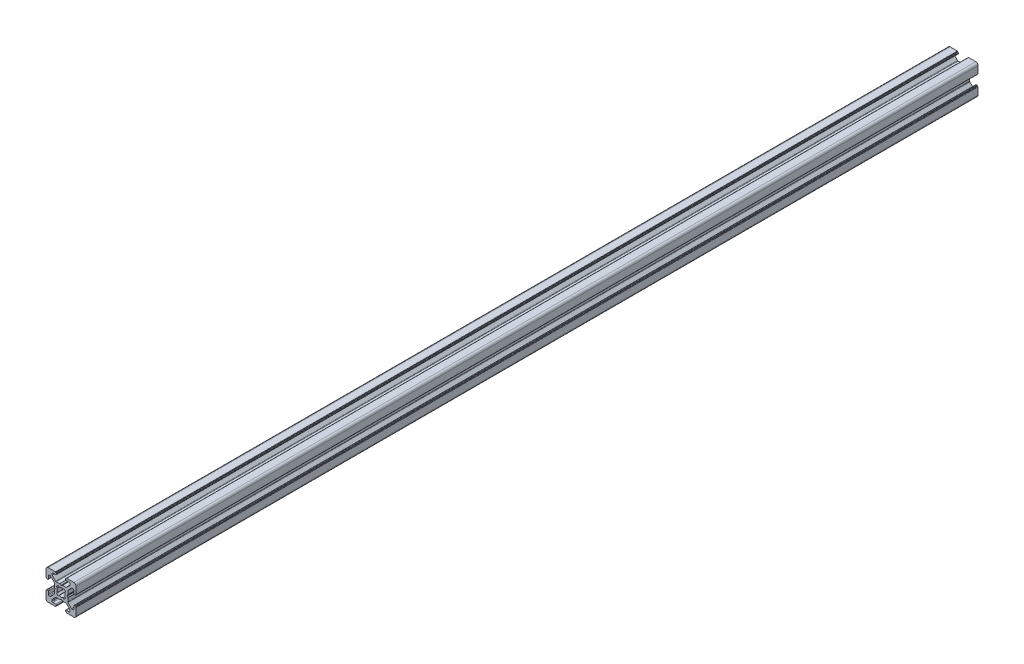
SolidWorks part; units mm, degrees
ref_plane "Front Plane" through (0, 0, 0) normal (0, 0, 1) x (1, 0, 0)
ref_plane "Top Plane" through (0, 0, 0) normal (0, 1, 0) x (1, 0, 0)
ref_plane "Right Plane" through (0, 0, 0) normal (1, 0, 0) x (0, 0, -1)
sketch "Sketch1" plane through (0, 0, 0) normal (0, 0, 1) x (1, 0, 0)
  line L0 (0, 13.3675) -> (0, -10.9159) construction
  line L1 (-12.9725, 0) -> (15.1887, 0) construction
  line L2 (-3.5, 8.5) -> (-5.5, 8.5)
  line L3 (-3.55, 9.7) -> (-3.55, 9.8)
  line L4 (-6, 7.2678) -> (-6, 8)
  line L5 (-7.2678, 6) -> (-8, 6)
  line L6 (-3.75, 10) -> (-8.5, 10)
  line L7 (-9.7, 3.55) -> (-9.8, 3.55)
  line L8 (-9.5, 3.2) -> (-9.5, 3.35)
  line L9 (-9, 3) -> (-9.3, 3)
  line L10 (-4.4732, 0.8536) -> (-4.0381, 0.1)
  line L11 (-4.5, 3.2322) -> (-4.5, 0.9536)
  line L12 (-8.5, 3.5) -> (-8.5, 5.5)
  line L13 (-10, 3.75) -> (-10, 8.5)
  line L14 (-3.5858, 4.6464) -> (-5.8536, 6.9142)
  line L15 (-4.6464, 3.5858) -> (-6.9142, 5.8536)
  line L16 (-3.2, 9.5) -> (-3.35, 9.5)
  line L17 (-3, 9) -> (-3, 9.3)
  line L18 (-0.8536, 4.4732) -> (-0.1, 4.0381)
  line L19 (-3.2322, 4.5) -> (-0.9536, 4.5)
  line L20 (-1.2582, 2.4453) -> (-1.9139, 2.9896)
  line L21 (-2.4453, 1.2582) -> (-2.9922, 1.9099)
  line L22 (3.5, -8.5) -> (5.5, -8.5)
  line L23 (3.55, -9.7) -> (3.55, -9.8)
  line L24 (6, -7.2678) -> (6, -8)
  line L25 (7.2678, -6) -> (8, -6)
  line L26 (3.75, -10) -> (8.5, -10)
  line L27 (9.7, -3.55) -> (9.8, -3.55)
  line L28 (9.5, -3.2) -> (9.5, -3.35)
  line L29 (9, -3) -> (9.3, -3)
  line L30 (4.4732, -0.8536) -> (4.0381, -0.1)
  line L31 (4.5, -3.2322) -> (4.5, -0.9536)
  line L32 (8.5, -3.5) -> (8.5, -5.5)
  line L33 (10, -3.75) -> (10, -8.5)
  line L34 (3.5858, -4.6464) -> (5.8536, -6.9142)
  line L35 (4.6464, -3.5858) -> (6.9142, -5.8536)
  line L36 (3.2, -9.5) -> (3.35, -9.5)
  line L37 (3, -9) -> (3, -9.3)
  line L38 (0.8536, -4.4732) -> (0.1, -4.0381)
  line L39 (3.2322, -4.5) -> (0.9536, -4.5)
  line L40 (1.2582, -2.4453) -> (1.9139, -2.9896)
  line L41 (2.4453, -1.2582) -> (2.9922, -1.9099)
  line L42 (-2.4453, -1.2582) -> (-2.9922, -1.9099)
  line L43 (-1.2582, -2.4453) -> (-1.9139, -2.9896)
  line L44 (-3.2322, -4.5) -> (-0.9536, -4.5)
  line L45 (-0.8536, -4.4732) -> (-0.1, -4.0381)
  line L46 (-3, -9) -> (-3, -9.3)
  line L47 (-3.2, -9.5) -> (-3.35, -9.5)
  line L48 (-4.6464, -3.5858) -> (-6.9142, -5.8536)
  line L49 (-3.5858, -4.6464) -> (-5.8536, -6.9142)
  line L50 (-10, -3.75) -> (-10, -8.5)
  line L51 (-8.5, -3.5) -> (-8.5, -5.5)
  line L52 (-4.5, -3.2322) -> (-4.5, -0.9536)
  line L53 (-4.4732, -0.8536) -> (-4.0381, -0.1)
  line L54 (-9, -3) -> (-9.3, -3)
  line L55 (-9.5, -3.2) -> (-9.5, -3.35)
  line L56 (-9.7, -3.55) -> (-9.8, -3.55)
  line L57 (2.4453, 1.2582) -> (2.9922, 1.9099)
  line L58 (1.2582, 2.4453) -> (1.9139, 2.9896)
  line L59 (3.2322, 4.5) -> (0.9536, 4.5)
  line L60 (0.8536, 4.4732) -> (0.1, 4.0381)
  line L61 (-3.75, -10) -> (-8.5, -10)
  line L62 (-7.2678, -6) -> (-8, -6)
  line L63 (-6, -7.2678) -> (-6, -8)
  line L64 (3, 9) -> (3, 9.3)
  line L65 (3.2, 9.5) -> (3.35, 9.5)
  line L66 (4.6464, 3.5858) -> (6.9142, 5.8536)
  line L67 (3.5858, 4.6464) -> (5.8536, 6.9142)
  line L68 (10, 3.75) -> (10, 8.5)
  line L69 (8.5, 3.5) -> (8.5, 5.5)
  line L70 (4.5, 3.2322) -> (4.5, 0.9536)
  line L71 (4.4732, 0.8536) -> (4.0381, 0.1)
  line L72 (9, 3) -> (9.3, 3)
  line L73 (9.5, 3.2) -> (9.5, 3.35)
  line L74 (9.7, 3.55) -> (9.8, 3.55)
  line L75 (3.75, 10) -> (8.5, 10)
  line L76 (7.2678, 6) -> (8, 6)
  line L77 (6, 7.2678) -> (6, 8)
  line L78 (3.55, 9.7) -> (3.55, 9.8)
  line L79 (3.5, 8.5) -> (5.5, 8.5)
  line L80 (-3.55, -9.7) -> (-3.55, -9.8)
  line L81 (-3.5, -8.5) -> (-5.5, -8.5)
  arc A0 (-10, 8.5) -> (-8.5, 10) centre (-8.5, 8.5) cw
  arc A1 (-8.5, 5.5) -> (-8, 6) centre (-8, 5.5) cw
  arc A2 (-7.2678, 6) -> (-6.9142, 5.8536) centre (-7.2678, 5.5) cw
  arc A3 (-5.8536, 6.9142) -> (-6, 7.2678) centre (-5.5, 7.2678) cw
  arc A4 (-6, 8) -> (-5.5, 8.5) centre (-5.5, 8) cw
  arc A5 (-9.7, 3.55) -> (-9.5, 3.35) centre (-9.7, 3.35) cw
  arc A6 (-9.8, 3.55) -> (-10, 3.75) centre (-9.8, 3.75) cw
  arc A7 (-9.3, 3) -> (-9.5, 3.2) centre (-9.3, 3.2) cw
  arc A8 (-8.5, 3.5) -> (-9, 3) centre (-9, 3.5) cw
  arc A9 (-4.6464, 3.5858) -> (-4.5, 3.2322) centre (-5, 3.2322) cw
  arc A10 (-4.4732, 0.8536) -> (-4.5, 0.9536) centre (-4.3, 0.9536) cw
  arc A11 (-4.0381, 0.1) -> (-4.0381, -0.1) centre (-4.2113, 0) cw
  arc A12 (-3.2, 9.5) -> (-3, 9.3) centre (-3.2, 9.3) cw
  arc A13 (-0.9536, 4.5) -> (-0.8536, 4.4732) centre (-0.9536, 4.3) cw
  arc A14 (-2.9922, 1.9099) -> (-1.9139, 2.9896) centre (0, 0) cw
  arc A15 (-3.2322, 4.5) -> (-3.5858, 4.6464) centre (-3.2322, 5) cw
  arc A16 (-3.75, 10) -> (-3.55, 9.8) centre (-3.75, 9.8) cw
  arc A17 (-3.35, 9.5) -> (-3.55, 9.7) centre (-3.35, 9.7) cw
  arc A18 (2.4453, -1.2582) -> (2.4453, 1.2582) centre (0, 0) ccw
  arc A19 (-3, 9) -> (-3.5, 8.5) centre (-3.5, 9) cw
  arc A20 (-2.4453, -1.2582) -> (-2.4453, 1.2582) centre (0, 0) cw
  arc A21 (10, -8.5) -> (8.5, -10) centre (8.5, -8.5) cw
  arc A22 (8.5, -5.5) -> (8, -6) centre (8, -5.5) cw
  arc A23 (7.2678, -6) -> (6.9142, -5.8536) centre (7.2678, -5.5) cw
  arc A24 (5.8536, -6.9142) -> (6, -7.2678) centre (5.5, -7.2678) cw
  arc A25 (6, -8) -> (5.5, -8.5) centre (5.5, -8) cw
  arc A26 (9.7, -3.55) -> (9.5, -3.35) centre (9.7, -3.35) cw
  arc A27 (9.8, -3.55) -> (10, -3.75) centre (9.8, -3.75) cw
  arc A28 (9.3, -3) -> (9.5, -3.2) centre (9.3, -3.2) cw
  arc A29 (8.5, -3.5) -> (9, -3) centre (9, -3.5) cw
  arc A30 (4.6464, -3.5858) -> (4.5, -3.2322) centre (5, -3.2322) cw
  arc A31 (4.4732, -0.8536) -> (4.5, -0.9536) centre (4.3, -0.9536) cw
  arc A32 (3.2, -9.5) -> (3, -9.3) centre (3.2, -9.3) cw
  arc A33 (-0.1, -4.0381) -> (0.1, -4.0381) centre (0, -4.2113) cw
  arc A34 (0.9536, -4.5) -> (0.8536, -4.4732) centre (0.9536, -4.3) cw
  arc A35 (2.9922, -1.9099) -> (1.9139, -2.9896) centre (0, 0) cw
  arc A36 (1.2582, -2.4453) -> (-1.2582, -2.4453) centre (0, 0) cw
  arc A37 (3.2322, -4.5) -> (3.5858, -4.6464) centre (3.2322, -5) cw
  arc A38 (3.75, -10) -> (3.55, -9.8) centre (3.75, -9.8) cw
  arc A39 (3.35, -9.5) -> (3.55, -9.7) centre (3.35, -9.7) cw
  arc A40 (3, -9) -> (3.5, -8.5) centre (3.5, -9) cw
  arc A41 (-3, -9) -> (-3.5, -8.5) centre (-3.5, -9) ccw
  arc A42 (-3.35, -9.5) -> (-3.55, -9.7) centre (-3.35, -9.7) ccw
  arc A43 (-3.75, -10) -> (-3.55, -9.8) centre (-3.75, -9.8) ccw
  arc A44 (-3.2322, -4.5) -> (-3.5858, -4.6464) centre (-3.2322, -5) ccw
  arc A45 (-2.9922, -1.9099) -> (-1.9139, -2.9896) centre (0, 0) ccw
  arc A46 (-0.9536, -4.5) -> (-0.8536, -4.4732) centre (-0.9536, -4.3) ccw
  arc A47 (-3.2, -9.5) -> (-3, -9.3) centre (-3.2, -9.3) ccw
  arc A48 (-4.4732, -0.8536) -> (-4.5, -0.9536) centre (-4.3, -0.9536) ccw
  arc A49 (3, 9) -> (3.5, 8.5) centre (3.5, 9) ccw
  arc A50 (3.35, 9.5) -> (3.55, 9.7) centre (3.35, 9.7) ccw
  arc A51 (3.75, 10) -> (3.55, 9.8) centre (3.75, 9.8) ccw
  arc A52 (3.2322, 4.5) -> (3.5858, 4.6464) centre (3.2322, 5) ccw
  arc A53 (1.2582, 2.4453) -> (-1.2582, 2.4453) centre (0, 0) ccw
  arc A54 (-4.6464, -3.5858) -> (-4.5, -3.2322) centre (-5, -3.2322) ccw
  arc A55 (-8.5, -3.5) -> (-9, -3) centre (-9, -3.5) ccw
  arc A56 (-9.3, -3) -> (-9.5, -3.2) centre (-9.3, -3.2) ccw
  arc A57 (-9.8, -3.55) -> (-10, -3.75) centre (-9.8, -3.75) ccw
  arc A58 (-9.7, -3.55) -> (-9.5, -3.35) centre (-9.7, -3.35) ccw
  arc A59 (-6, -8) -> (-5.5, -8.5) centre (-5.5, -8) ccw
  arc A60 (2.9922, 1.9099) -> (1.9139, 2.9896) centre (0, 0) ccw
  arc A61 (0.9536, 4.5) -> (0.8536, 4.4732) centre (0.9536, 4.3) ccw
  arc A62 (-0.1, 4.0381) -> (0.1, 4.0381) centre (0, 4.2113) ccw
  arc A63 (-5.8536, -6.9142) -> (-6, -7.2678) centre (-5.5, -7.2678) ccw
  arc A64 (-7.2678, -6) -> (-6.9142, -5.8536) centre (-7.2678, -5.5) ccw
  arc A65 (-8.5, -5.5) -> (-8, -6) centre (-8, -5.5) ccw
  arc A66 (-10, -8.5) -> (-8.5, -10) centre (-8.5, -8.5) ccw
  arc A67 (3.2, 9.5) -> (3, 9.3) centre (3.2, 9.3) ccw
  arc A68 (4.0381, 0.1) -> (4.0381, -0.1) centre (4.2113, 0) ccw
  arc A69 (4.4732, 0.8536) -> (4.5, 0.9536) centre (4.3, 0.9536) ccw
  arc A70 (4.6464, 3.5858) -> (4.5, 3.2322) centre (5, 3.2322) ccw
  arc A71 (8.5, 3.5) -> (9, 3) centre (9, 3.5) ccw
  arc A72 (9.3, 3) -> (9.5, 3.2) centre (9.3, 3.2) ccw
  arc A73 (9.8, 3.55) -> (10, 3.75) centre (9.8, 3.75) ccw
  arc A74 (9.7, 3.55) -> (9.5, 3.35) centre (9.7, 3.35) ccw
  arc A75 (6, 8) -> (5.5, 8.5) centre (5.5, 8) ccw
  arc A76 (5.8536, 6.9142) -> (6, 7.2678) centre (5.5, 7.2678) ccw
  arc A77 (7.2678, 6) -> (6.9142, 5.8536) centre (7.2678, 5.5) ccw
  arc A78 (8.5, 5.5) -> (8, 6) centre (8, 5.5) ccw
  arc A79 (10, 8.5) -> (8.5, 10) centre (8.5, 8.5) ccw
  dimension "D4" = 5.5
  dimension "D1" = 6
  dimension "D2" = 20
  dimension "D3" = 20
  dimension "D5" = 5.5
  dimension "D6" = 10
  dimension "D7" = 6
  dimension "D8" = 6
  dimension "D9" = 6
extrude "Extrude1" add sketch "Sketch1" along normal blind 600
